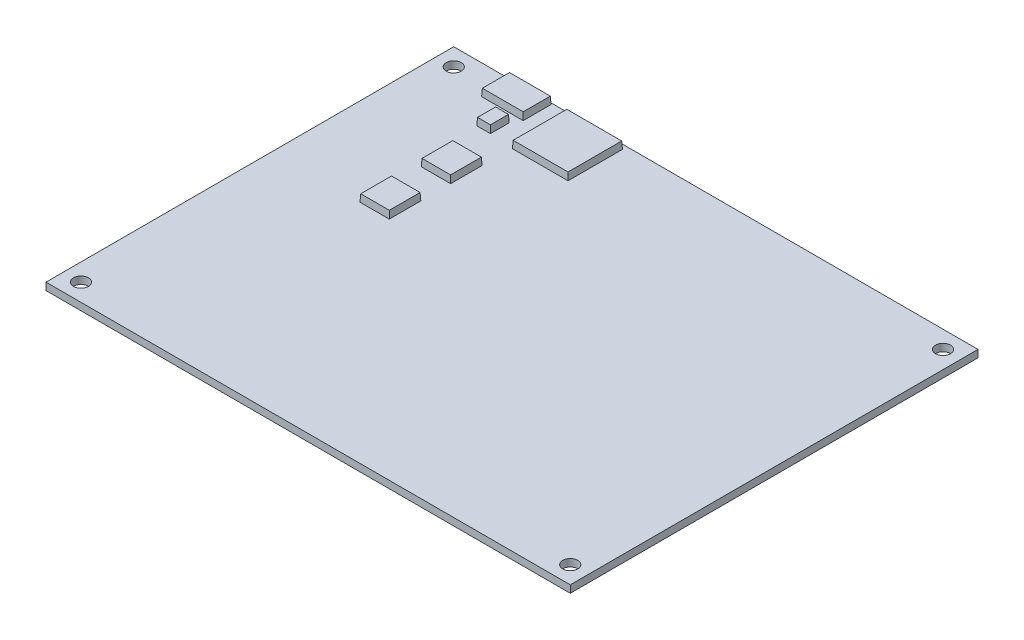
SolidWorks part; units mm, degrees
ref_plane "Front Plane" through (0, 0, 0) normal (0, 0, 1) x (1, 0, 0)
ref_plane "Top Plane" through (0, 0, 0) normal (0, 1, 0) x (1, 0, 0)
ref_plane "Right Plane" through (0, 0, 0) normal (1, 0, 0) x (0, 0, -1)
sketch "Sketch1" plane through (0, 0, 0) normal (0, 1, 0) x (1, 0, 0)
  line L1 (-55.88, -44.45) -> (49.53, -44.45)
  line L2 (-57.15, -6.35) -> (-57.15, 44.45)
  line L3 (-57.15, 44.45) -> (57.15, 44.45)
  line L4 (57.15, -6.35) -> (57.15, 44.45)
  line L5 (-57.15, -44.45) -> (57.15, 44.45) construction
  line L6 (-57.15, 44.45) -> (57.15, -44.45) construction
  line L7 (-57.15, -44.45) -> (-55.88, -44.45)
  line L8 (-57.15, -44.45) -> (-57.15, -6.35)
  line L11 (57.15, -44.45) -> (49.53, -44.45)
  line L12 (57.15, -44.45) -> (57.15, -6.35)
  point P0 (0, 0)
  dimension "D1" = 114.3
  dimension "D2" = 88.9
extrude "Extrude1" add sketch "Sketch1" along normal blind 1.6002
hole_wizard "#4 Clearance Hole1" positions "Sketch4" profile "Sketch3" hole size "#4" standard "Ansi Inch" end condition through all
sketch "Sketch4" plane through (0, 1.6002, 0) normal (0, 1, 0) x (-1, 0, 0)
  line L0 (57.15, -44.45) -> (57.15, 44.45) construction
  line L1 (57.15, 44.45) -> (-57.15, 44.45) construction
  point P0 (53.34, -40.64)
  point P1 (-53.34, -40.64)
  point P3 (-53.34, 40.64)
  point P5 (53.34, 40.64)
  dimension "D1" = 110.49
  dimension "D2" = 3.81
  dimension "D3" = 3.81
  dimension "D4" = 85.09
sketch "Sketch3" plane through (-53.34, 1.6002, -40.64) normal (1, 0, 0) x (0, 0, 1)
  line L0 (0, 0) -> (0, 1.6002)
  line L1 (0, 1.6002) -> (1.6319, 1.6002)
  line L2 (1.6319, 1.6002) -> (1.6319, 0)
  line L5 (1.6319, 0) -> (0, 0)
  line L11 (0, -6.35) -> (0, 107.95) construction
  dimension "Thru Hole Dia." = 3.2639
  dimension "Thru Hole Depth" = 1.6002
sketch "Sketch5" plane through (0, 1.6002, 0) normal (0, 1, 0) x (1, 0, 0)
  line L1 (-38.0207, 25.1215) -> (-31.6279, 25.1215)
  line L2 (-38.0207, 25.1215) -> (-38.0207, 18.2413)
  line L3 (-38.0207, 18.2413) -> (-31.6279, 18.2413)
  line L4 (-31.6279, 25.1215) -> (-31.6279, 18.2413)
  line L5 (-44.6927, 44.1461) -> (-35.6249, 44.1461)
  line L6 (-44.6927, 44.1461) -> (-44.6927, 38.0619)
  line L7 (-44.6927, 38.0619) -> (-35.6249, 38.0619)
  line L8 (-35.6249, 44.1461) -> (-35.6249, 38.0619)
  line L9 (-38.0207, 11.7502) -> (-31.6279, 11.7502)
  line L10 (-38.0207, 11.7502) -> (-38.0207, 4.87)
  line L11 (-38.0207, 4.87) -> (-31.6279, 4.87)
  line L12 (-31.6279, 11.7502) -> (-31.6279, 4.87)
  line L13 (-31.5035, 43.4599) -> (-19.3772, 43.4599)
  line L14 (-31.5035, 43.4599) -> (-31.5035, 31.5915)
  line L15 (-31.5035, 31.5915) -> (-19.3772, 31.5915)
  line L16 (-19.3772, 43.4599) -> (-19.3772, 31.5915)
  line L17 (-39.72, 36.1313) -> (-36.7364, 36.1313)
  line L18 (-39.72, 36.1313) -> (-39.72, 32.0362)
  line L19 (-39.72, 32.0362) -> (-36.7364, 32.0362)
  line L20 (-36.7364, 36.1313) -> (-36.7364, 32.0362)
extrude "Boss-Extrude1" add sketch "Sketch5" along normal blind 1.5875 draft 3
